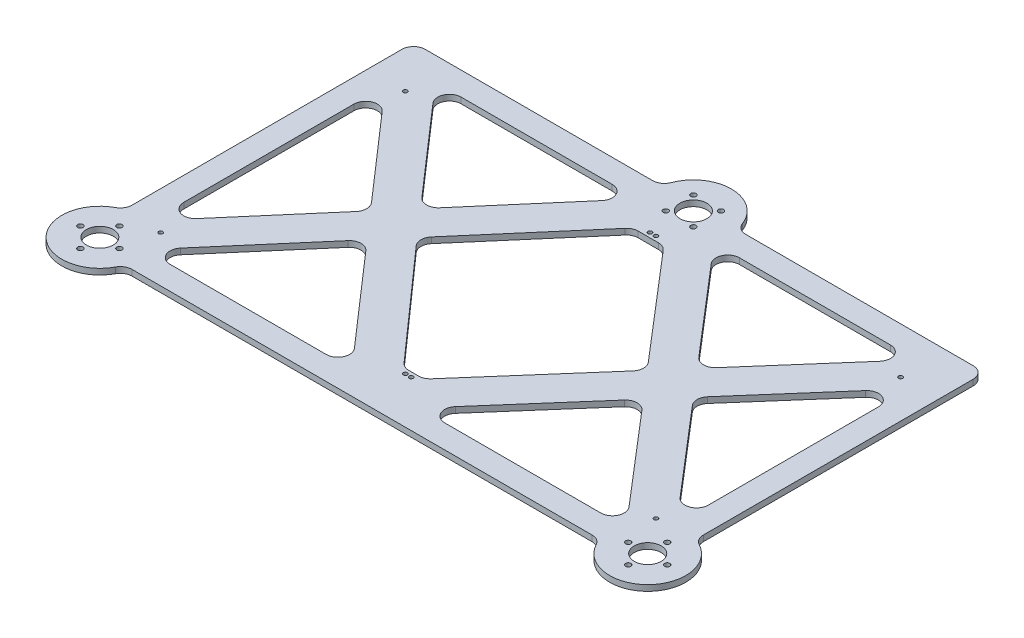
SolidWorks part; units mm, degrees
ref_plane "Plan de face" through (0, 0, 0) normal (0, 0, 1) x (1, 0, 0)
ref_plane "Plan de dessus" through (0, 0, 0) normal (0, 1, 0) x (1, 0, 0)
ref_plane "Plan de droite" through (0, 0, 0) normal (1, 0, 0) x (0, 0, -1)
sketch "Esquisse1" plane through (0, 0, 0) normal (0, 1, 0) x (1, 0, 0)
  line L0 (0, -114) -> (0, 134) construction
  line L1 (-200, 100) -> (200, 100) construction
  line L2 (-200, 100) -> (-200, -100) construction
  line L3 (-200, -100) -> (200, -100) construction
  line L4 (200, 100) -> (200, -100) construction
  line L5 (-214, 114) -> (214, 114) construction
  line L6 (-214, 114) -> (-214, -114) construction
  line L7 (-214, -114) -> (214, -114) construction
  line L8 (214, 114) -> (214, -114) construction
  line L9 (-214, 0) -> (214, 0) construction
  line L10 (-200, -100) -> (-234, -134) construction
  line L11 (200, -100) -> (234, -134) construction
  line L12 (0, 114) -> (0, 139) construction
  line L13 (-234, 134) -> (-21.9374, 134) construction
  line L14 (-234, 134) -> (-234, -117.33) construction
  line L15 (-211.5, -134) -> (211.5, -134) construction
  line L16 (234, 134) -> (234, -117.33) construction
  line L17 (21.9374, 134) -> (234, 134) construction
  line L18 (-190.8815, 107.4229) -> (-125.7888, 32.8723)
  line L19 (-183.3488, 124) -> (-54.3555, 124)
  line L20 (-196.5, -144) -> (196.5, -144)
  line L21 (54.3555, 124) -> (183.3488, 124)
  line L22 (125.7888, 32.8723) -> (190.8815, 107.4229)
  line L23 (-244, 134) -> (-244, -96.5)
  line L24 (-234, 144) -> (-39.7649, 144)
  line L25 (-183.9302, -124) -> (-50.6512, -124)
  line L26 (39.7649, 144) -> (234, 144)
  line L27 (244, 134) -> (244, -96.5)
  line L28 (-234, -134) -> (0, 139) construction
  line L29 (-244, 144) -> (-21.9374, 144) construction
  line L30 (-224, 124) -> (-21.9374, 124) construction
  line L31 (21.9374, 124) -> (224, 124) construction
  line L32 (21.9374, 144) -> (244, 144) construction
  line L33 (244, 144) -> (244, -111.5) construction
  line L34 (224, 124) -> (224, -111.5) construction
  line L35 (-211.5, -124) -> (211.5, -124) construction
  line L36 (-211.5, -144) -> (211.5, -144) construction
  line L37 (-224, 124) -> (-224, -111.5) construction
  line L38 (-244, 144) -> (-244, -111.5) construction
  line L39 (0, 139) -> (234, -134) construction
  line L40 (-234, 134) -> (0, -134) construction
  line L41 (46.7629, 107.4921) -> (110.6635, 32.9414)
  line L42 (0, -134) -> (234, 134) construction
  line L43 (-206.4074, -78.7598) -> (-143.5453, -5.4206)
  line L44 (-191.5228, -107.4921) -> (-125.4992, -30.4645)
  line L45 (16.2371, 97.0079) -> (92.6174, 7.8975)
  line L46 (-224, 73.0832) -> (-224, -72.2519)
  line L47 (-110.6635, 32.9414) -> (-46.7629, 107.4921)
  line L48 (-2.5, -104.5) -> (2.5, -104.5) construction
  line L49 (12.3256, -97.0771) -> (92.5575, -5.1875)
  line L50 (224, 73.0832) -> (224, -72.2519)
  line L51 (0, -111.1935) -> (222.7009, 143.8656) construction
  line L52 (125.4992, -30.4645) -> (191.5228, -107.4921)
  line L53 (143.6051, 7.6644) -> (206.4673, 79.6603)
  line L54 (0, 139) -> (-15.9099, 123.0901) construction
  line L55 (143.5453, -5.4206) -> (206.4074, -78.7598)
  line L56 (43.1185, -107.4229) -> (110.3739, -30.3954)
  line L57 (-234, 134) -> (-234, -111.5) construction
  line L58 (50.6512, -124) -> (183.9302, -124)
  line L59 (-92.5055, -5.2466) -> (-10.9897, -97.1362)
  line L60 (-92.6174, 7.8975) -> (-16.2371, 97.0079)
  line L61 (-222.7009, 143.8656) -> (0, -111.1935) construction
  line L62 (-110.3739, -30.3954) -> (-43.1185, -107.4229)
  line L63 (-206.4673, 79.6603) -> (-143.6051, 7.6644)
  line L64 (234, 134) -> (234, -111.5) construction
  line L65 (-8.6445, 100.5) -> (8.6445, 100.5)
  line L66 (-3.509, -100.5) -> (4.7928, -100.5)
  circle A0 centre (234, -134) radius 22.5 construction
  circle A1 centre (-234, -134) radius 22.5 construction
  circle A2 centre (-2.5, 104.5) radius 1.75
  circle A3 centre (-211.5, 104.5) radius 1.75
  circle A4 centre (211.5, 104.5) radius 1.75
  circle A5 centre (2.5, 104.5) radius 1.75
  circle A6 centre (2.5, -104.5) radius 1.75
  circle A7 centre (-2.5, -104.5) radius 1.75
  circle A8 centre (-211.5, -104.5) radius 1.75
  circle A9 centre (211.5, -104.5) radius 1.75
  circle A10 centre (0, 139) radius 22.5 construction
  arc A11 (-8.6445, 100.5) -> (-16.2371, 97.0079) centre (-8.6445, 90.5) ccw
  arc A12 (244, -96.5) -> (249.2941, -105.3235) centre (254, -96.5) ccw
  arc A13 (30.4085, 150.4706) -> (-30.4085, 150.4706) centre (0, 139) ccw
  circle A14 centre (0, 139) radius 11.5
  circle A15 centre (-234, -134) radius 11.5
  circle A16 centre (234, -134) radius 11.5
  arc A17 (8.6445, 100.5) -> (16.2371, 97.0079) centre (8.6445, 90.5) cw
  circle A18 centre (0, 139) radius 32.5 construction
  arc A19 (205.3235, -149.2941) -> (249.2941, -105.3235) centre (234, -134) ccw
  arc A20 (4.7928, -100.5) -> (12.3256, -97.0771) centre (4.7928, -90.5) ccw
  arc A21 (-249.2941, -105.3235) -> (-205.3235, -149.2941) centre (-234, -134) ccw
  arc A22 (183.9302, -124) -> (191.5228, -107.4921) centre (183.9302, -114) ccw
  arc A23 (-3.509, -100.5) -> (-10.9897, -97.1362) centre (-3.509, -90.5) cw
  arc A24 (205.3235, -149.2941) -> (196.5, -144) centre (196.5, -154) ccw
  arc A25 (-196.5, -144) -> (-205.3235, -149.2941) centre (-196.5, -154) ccw
  arc A26 (-244, -96.5) -> (-249.2941, -105.3235) centre (-254, -96.5) cw
  arc A27 (-206.4074, -78.7598) -> (-224, -72.2519) centre (-214, -72.2519) cw
  arc A28 (-206.4673, 79.6603) -> (-224, 73.0832) centre (-214, 73.0832) ccw
  arc A29 (-183.3488, 124) -> (-190.8815, 107.4229) centre (-183.3488, 114) ccw
  arc A30 (-244, 134) -> (-234, 144) centre (-234, 134) cw
  arc A31 (234, 144) -> (244, 134) centre (234, 134) cw
  arc A32 (39.7649, 144) -> (30.4085, 150.4706) centre (39.7649, 154) cw
  arc A33 (-39.7649, 144) -> (-30.4085, 150.4706) centre (-39.7649, 154) ccw
  arc A34 (-46.7629, 107.4921) -> (-54.3555, 124) centre (-54.3555, 114) ccw
  arc A35 (54.3555, 124) -> (46.7629, 107.4921) centre (54.3555, 114) ccw
  arc A36 (190.8815, 107.4229) -> (183.3488, 124) centre (183.3488, 114) ccw
  arc A37 (206.4074, -78.7598) -> (224, -72.2519) centre (214, -72.2519) ccw
  arc A38 (224, 73.0832) -> (206.4673, 79.6603) centre (214, 73.0832) ccw
  arc A39 (143.6051, 7.6644) -> (143.5453, -5.4206) centre (151.1378, 1.0873) ccw
  arc A40 (125.7888, 32.8723) -> (110.6635, 32.9414) centre (118.2561, 39.4494) cw
  arc A41 (92.5575, -5.1875) -> (92.6174, 7.8975) centre (85.0248, 1.3896) ccw
  arc A42 (-110.6635, 32.9414) -> (-125.7888, 32.8723) centre (-118.2561, 39.4494) cw
  arc A43 (-143.6051, 7.6644) -> (-143.5453, -5.4206) centre (-151.1378, 1.0873) cw
  arc A44 (-92.5055, -5.2466) -> (-92.6174, 7.8975) centre (-85.0248, 1.3896) cw
  arc A45 (125.4992, -30.4645) -> (110.3739, -30.3954) centre (117.9066, -36.9725) ccw
  arc A46 (-125.4992, -30.4645) -> (-110.3739, -30.3954) centre (-117.9066, -36.9725) cw
  arc A47 (43.1185, -107.4229) -> (50.6512, -124) centre (50.6512, -114) ccw
  arc A48 (-43.1185, -107.4229) -> (-50.6512, -124) centre (-50.6512, -114) cw
  arc A51 (-183.9302, -124) -> (-191.5228, -107.4921) centre (-183.9302, -114) cw
  circle A52 centre (0, 139) radius 16.67 construction
  circle A53 centre (-11.7875, 127.2125) radius 2.25
  circle A54 centre (-11.7875, 150.7875) radius 2.25
  circle A55 centre (11.7875, 150.7875) radius 2.25
  circle A56 centre (11.7875, 127.2125) radius 2.25
  circle A57 centre (-234, -134) radius 16.67 construction
  circle A58 centre (-234, -117.33) radius 2.25
  circle A59 centre (-217.33, -134) radius 2.25
  circle A60 centre (-234, -150.67) radius 2.25
  circle A61 centre (-250.67, -134) radius 2.25
  circle A62 centre (234, -134) radius 16.67 construction
  circle A63 centre (234, -117.33) radius 2.25
  circle A64 centre (250.67, -134) radius 2.25
  circle A65 centre (234, -150.67) radius 2.25
  circle A66 centre (217.33, -134) radius 2.25
  point P76 (32.5, 139)
  point P78 (-245.2991, 124.1344)
  point P79 (266.5, -134)
  point P80 (0, -156.8065)
  point P83 (-201.5, -134)
  point P87 (-222.6112, -143.7619)
  point P88 (0, 115.9511)
  point P89 (222.6112, -143.7619)
  point P90 (-245.3888, -124.2381)
  point P91 (0, 162.0489)
  point P92 (245.3888, -124.2381)
  point P99 (245.2991, 124.1344)
  point P128 (-244, -103.0767)
  point P157 (137.9152, 1.1477)
  point P168 (-98.2924, 1.2767)
  point P175 (28.6444, -124)
  point P196 (0, 139)
  point P206 (-234, -134)
  point P216 (234, -134)
  point P218 (0, 139)
  dimension "D13" = 9.5
  dimension "D14" = 3.5
  dimension "D16" = 3.5
  dimension "D17" = 3.5
  dimension "D22" = 10
  dimension "D24" = 10
  dimension "D26" = 10
  dimension "D27" = 4
  dimension "D28" = 45
  dimension "D29" = 4
  dimension "D30" = 4
  dimension "D31" = 4
  dimension "D1" = 200
  dimension "D2" = 100
  dimension "D3" = 200
  dimension "D4" = 400
  dimension "D5" = 14
  dimension "D6" = 428
  dimension "D7" = 14
  dimension "D8" = 228
  dimension "D9" = 468
  dimension "D10" = 20
  dimension "D11" = 20
  dimension "D12" = 268
  dimension "D15" = 2.5
  dimension "D18" = 9.5
  dimension "D19" = 9.5
  dimension "D20" = 2.5
  dimension "D21" = 2.5
  dimension "D32" = 4
  dimension "D23" = 10
  dimension "D25" = 15
extrude "Boss.-Extru.1" add sketch "Esquisse1" along normal blind 5
